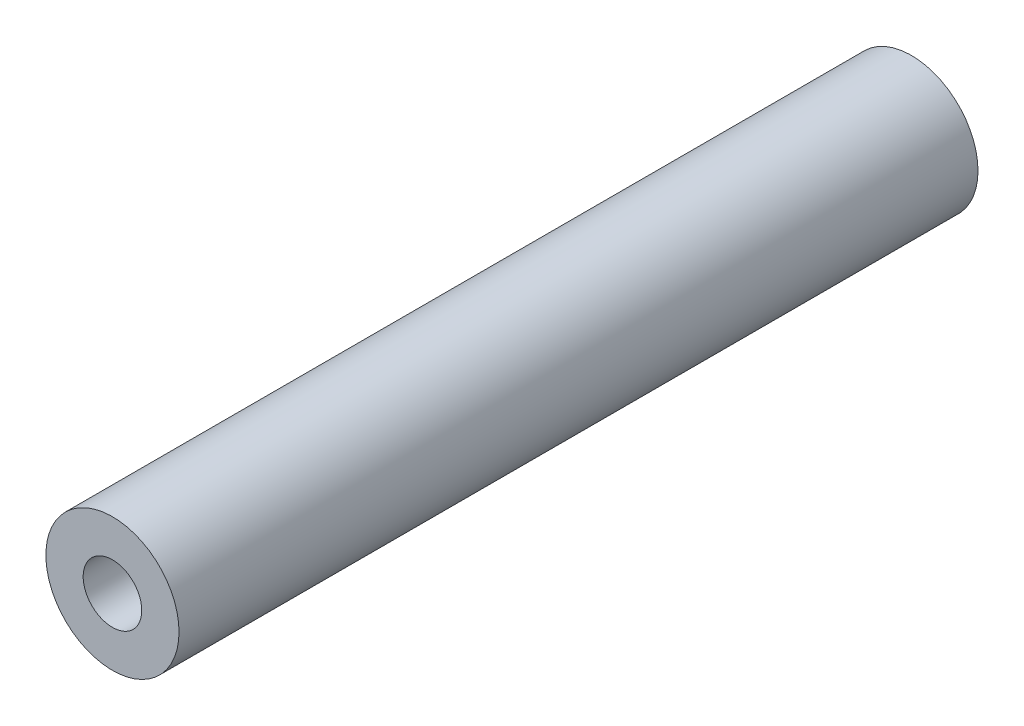
SolidWorks part; units mm, degrees
material "1.4310 (X10CrNi18-8)"
ref_plane "Front Plane" through (0, 0, 0) normal (0, 0, 1) x (1, 0, 0)
ref_plane "Top Plane" through (0, 0, 0) normal (0, 1, 0) x (1, 0, 0)
ref_plane "Right Plane" through (0, 0, 0) normal (1, 0, 0) x (0, 0, -1)
sketch "Sketch1" plane through (0, 0, 0) normal (0, 0, 1) x (1, 0, 0)
  circle A0 centre (0, 0) radius 3.175
  dimension "D1" = 6.35
extrude "Boss-Extrude1" add sketch "Sketch1" along normal blind 38.1
sketch "Sketch2" plane through (0, 0, 38.1) normal (0, 0, 1) x (1, 0, 0)
  circle A0 centre (0, 0) radius 1.397
  dimension "D1" = 2.794
extrude "Cut-Extrude1" cut sketch "Sketch2" against normal blind 5.08
